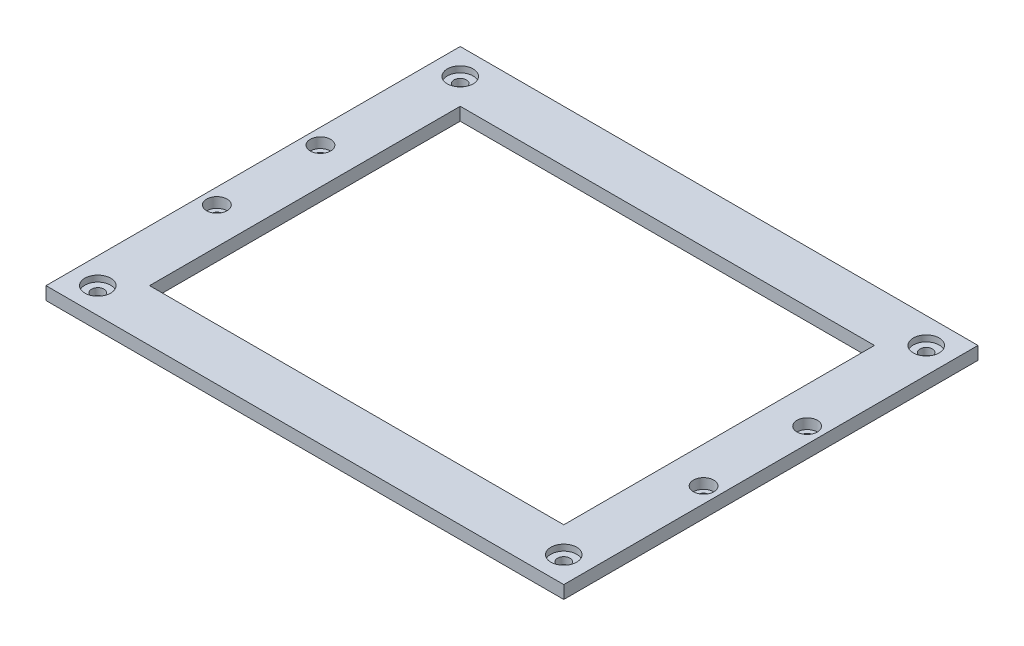
SolidWorks part; units mm, degrees
ref_plane "Front Plane" through (0, 0, 0) normal (0, 0, 1) x (1, 0, 0)
ref_plane "Top Plane" through (0, 0, 0) normal (0, 1, 0) x (1, 0, 0)
ref_plane "Right Plane" through (0, 0, 0) normal (1, 0, 0) x (0, 0, -1)
sketch "Sketch1" plane through (0, 0, 0) normal (0, 1, 0) x (1, 0, 0)
  line L1 (0, 0) -> (254, 0)
  line L2 (0, 0) -> (0, 203.2)
  line L3 (0, 203.2) -> (254, 203.2)
  line L4 (254, 0) -> (254, 203.2)
  line L5 (12.7, 190.5) -> (241.3, 190.5) construction
  line L6 (12.7, 190.5) -> (12.7, 12.7) construction
  line L7 (25.4, 177.8) -> (228.6, 177.8)
  line L8 (25.4, 177.8) -> (25.4, 25.4)
  line L9 (25.4, 25.4) -> (228.6, 25.4)
  line L10 (228.6, 177.8) -> (228.6, 25.4)
  line L11 (12.7, 12.7) -> (241.3, 12.7) construction
  line L12 (241.3, 190.5) -> (241.3, 12.7) construction
  circle A0 centre (12.7, 190.5) radius 3.05
  circle A1 centre (241.3, 190.5) radius 3.05
  circle A2 centre (241.3, 12.7) radius 3.05
  circle A3 centre (12.7, 12.7) radius 3.05
  dimension "D11" = 6.1
  dimension "D12" = 6.1
  dimension "D13" = 6.1
  dimension "D14" = 6.1
  dimension "D1" = 254
  dimension "D2" = 203.2
  dimension "D3" = 25.4
  dimension "D4" = 25.4
  dimension "D5" = 25.4
  dimension "D6" = 25.4
  dimension "D7" = 12.7
  dimension "D8" = 12.7
  dimension "D9" = 12.7
  dimension "D10" = 12.7
extrude "Boss-Extrude1" add sketch "Sketch1" along normal blind 6.35
sketch "Sketch2" plane through (0, 6.35, 0) normal (0, 1, 0) x (1, 0, 0)
  circle A0 centre (12.7, 190.5) radius 6.35
  circle A1 centre (241.3, 190.5) radius 6.35
  circle A2 centre (241.3, 12.7) radius 6.35
  circle A3 centre (12.7, 12.7) radius 6.35
  dimension "D1" = 12.7
  dimension "D2" = 12.7
  dimension "D3" = 12.7
  dimension "D4" = 12.7
extrude "Cut-Extrude1" cut sketch "Sketch2" against normal blind 3
hole_wizard "CBORE for M5 SHCS1" positions "Sketch3" profile "Sketch4" counterbore size "M5" standard "ANSI Metric" end condition through all
sketch "Sketch3" plane through (0, 6.35, 0) normal (0, 1, 0) x (1, 0, 0)
  line L0 (254, 0) -> (254, 203.2) construction
  line L1 (0, 0) -> (254, 0) construction
  line L2 (254, 203.2) -> (0, 203.2) construction
  line L3 (0, 203.2) -> (0, 0) construction
  point P0 (246.38, 76.2)
  point P2 (246.38, 127)
  point P4 (7.62, 76.2)
  point P6 (7.62, 127)
  dimension "D1" = 7.62
  dimension "D2" = 76.2
  dimension "D3" = 76.2
  dimension "D4" = 7.62
  dimension "D5" = 76.2
  dimension "D6" = 76.2
  dimension "D7" = 7.62
  dimension "D8" = 7.62
sketch "Sketch4" plane through (246.38, 6.35, -76.2) normal (1, 0, 0) x (0, 0, 1)
  line L0 (0, 0) -> (0, 6.35)
  line L1 (0, 6.35) -> (2.75, 6.35)
  line L3 (2.75, 6.35) -> (2.75, 5)
  line L4 (2.75, 5) -> (5, 5)
  line L5 (5, 5) -> (5, 0)
  line L7 (5, 0) -> (0, 0)
  line L11 (0, -6.35) -> (0, 107.95) construction
  dimension "Thru Hole Dia." = 5.5
  dimension "Thru Hole Depth" = 6.35
  dimension "C'Bore Dia." = 10
  dimension "C'Bore Depth" = 5
